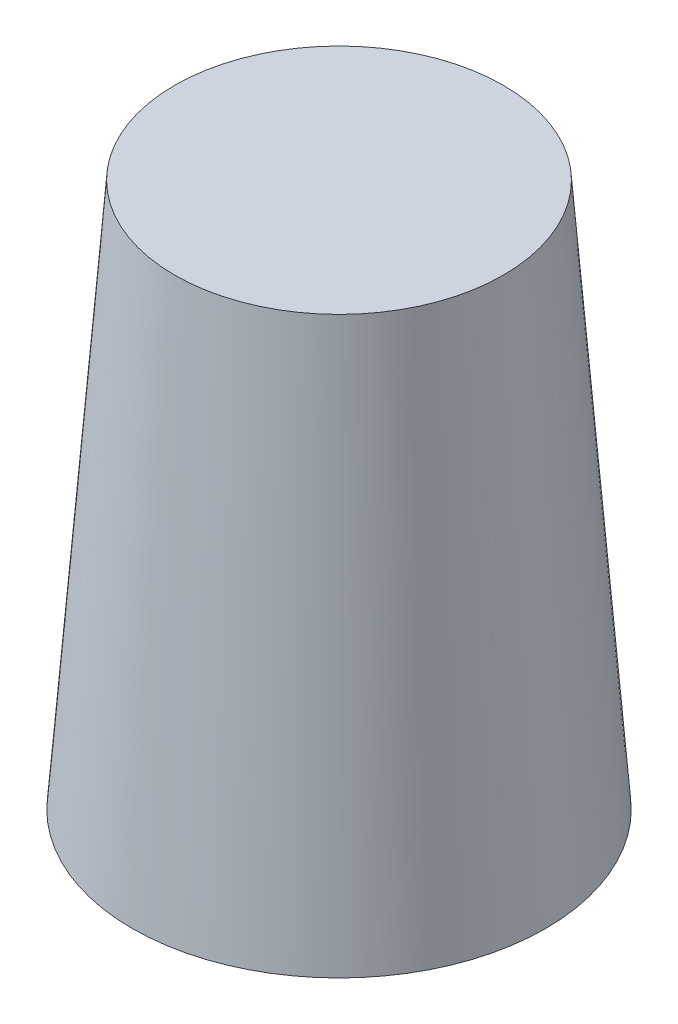
SolidWorks part; units mm, degrees
ref_plane "Front Plane" through (0, 0, 0) normal (0, 0, 1) x (1, 0, 0)
ref_plane "Top Plane" through (0, 0, 0) normal (0, 1, 0) x (1, 0, 0)
ref_plane "Right Plane" through (0, 0, 0) normal (1, 0, 0) x (0, 0, -1)
sketch "Sketch1" plane through (0, 0, 0) normal (0, 0, 1) x (1, 0, 0)
  line L0 (0, 53.7037) -> (0, -62.2963) construction
  line L1 (35, 53.7037) -> (44, -62.2963)
  line L2 (33.5, 53.7037) -> (42.6296, -62.2963)
  line L3 (42.6296, -62.2963) -> (44, -62.2963)
  line L4 (33.5, 53.7037) -> (35, 53.7037)
  dimension "D1" = 116
  dimension "D2" = 35
  dimension "D3" = 44
  dimension "D4" = 1.5
revolve "Revolve1" add sketch "Sketch1" angle 360 about L0
sketch "Sketch2" plane through (0, 53.7037, 0) normal (0, 1, 0) x (1, 0, 0)
  circle A0 centre (0, 0) radius 35
extrude "Boss-Extrude1" add sketch "Sketch2" against normal blind 1.5
fillet "Fillet1" radius 5 1 edges at (0, 52.2037, 33.6181)
